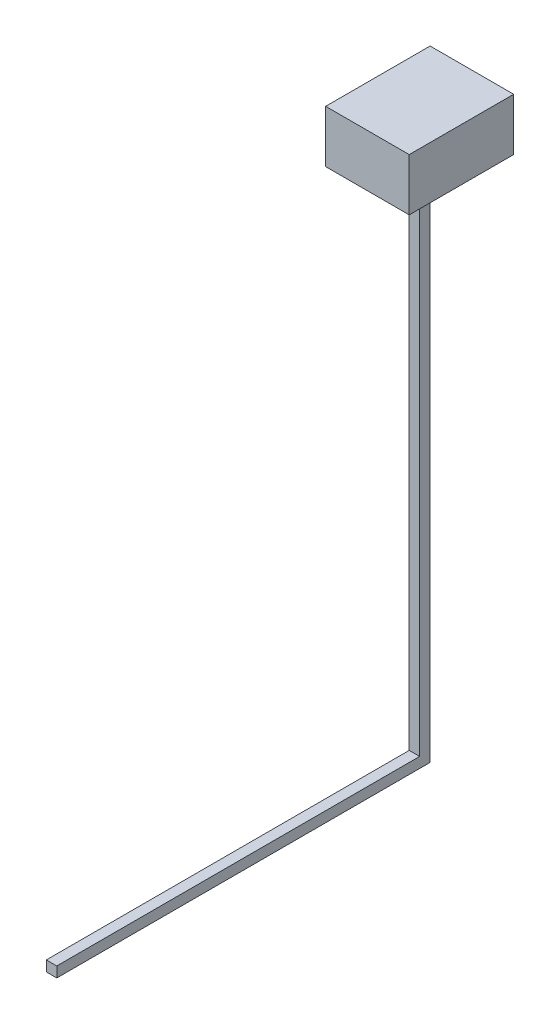
SolidWorks part; units mm, degrees
ref_plane "Front Plane" through (0, 0, 0) normal (0, 0, 1) x (1, 0, 0)
ref_plane "Top Plane" through (0, 0, 0) normal (0, 1, 0) x (1, 0, 0)
ref_plane "Right Plane" through (0, 0, 0) normal (1, 0, 0) x (0, 0, -1)
sketch "Sketch1" plane through (0, 0, 0) normal (1, 0, 0) x (0, 0, -1)
  line L0 (0, 0) -> (357.3607, 0)
  line L1 (357.3607, 0) -> (357.3607, 498.9143)
  line L2 (357.3607, 498.9143) -> (347.3607, 498.9143)
  line L3 (347.3607, 498.9143) -> (347.3607, 10)
  line L4 (347.3607, 10) -> (0, 10)
  line L5 (0, 10) -> (0, 0)
  dimension "D1" = 357.3607
  dimension "D2" = 498.9143
  dimension "D3" = 10
  dimension "D4" = 10
extrude "Extrude1" add sketch "Sketch1" along normal blind 10
sketch "Sketch2" plane through (0, 498.9143, 0) normal (0, 1, 0) x (-1, 0, 0)
  line L0 (-10, -347.3607) -> (0, -347.3607) construction
  line L1 (-45, -302.3607) -> (35, -302.3607)
  line L2 (-45, -302.3607) -> (-45, -402.3607)
  line L3 (-45, -402.3607) -> (35, -402.3607)
  line L4 (35, -302.3607) -> (35, -402.3607)
  line L5 (-10, -357.3607) -> (-10, -347.3607) construction
  dimension "D1" = 80
  dimension "D2" = 100
  dimension "D3" = 45
  dimension "D4" = 35
extrude "Extrude2" add sketch "Sketch2" along normal blind 50
